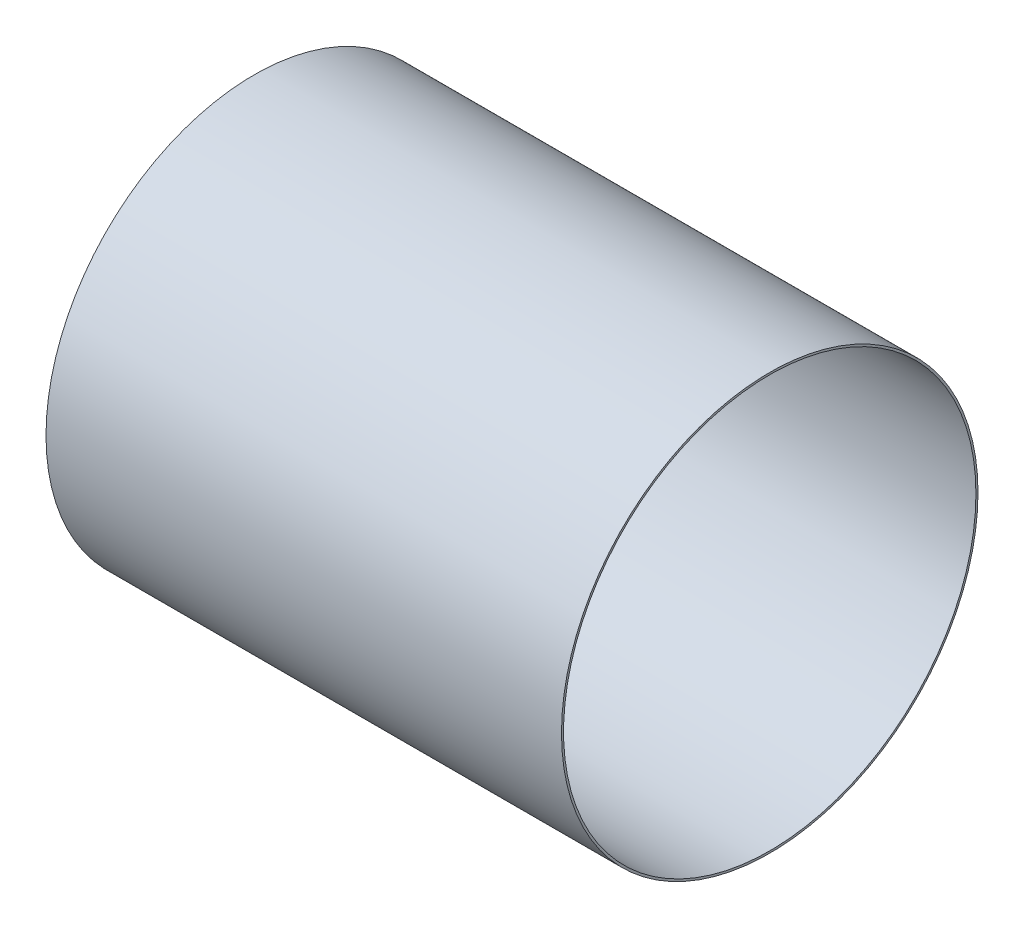
SolidWorks part; units mm, degrees
material "Gray Cast Iron"
ref_plane "Front Plane" through (0, 0, 0) normal (0, 0, 1) x (1, 0, 0)
ref_plane "Top Plane" through (0, 0, 0) normal (0, 1, 0) x (1, 0, 0)
ref_plane "Right Plane" through (0, 0, 0) normal (1, 0, 0) x (0, 0, -1)
sketch "Sketch1" plane through (0, 0, 0) normal (0, 0, 1) x (1, 0, 0)
  line L5 (0, 0) -> (250, 0)
  line L6 (0, 0) -> (0, 101)
  line L7 (0, 101) -> (250, 101)
  line L8 (250, 0) -> (250, 101)
revolve "Revolve1" add sketch "Sketch1" angle 360 about L7
sketch "Sketch2" plane through (250, 0, 0) normal (1, 0, 0) x (0, 0, -1)
  circle A2 centre (0, 101) radius 100
extrude "Cut-Extrude2" cut sketch "Sketch2" against normal blind 250
